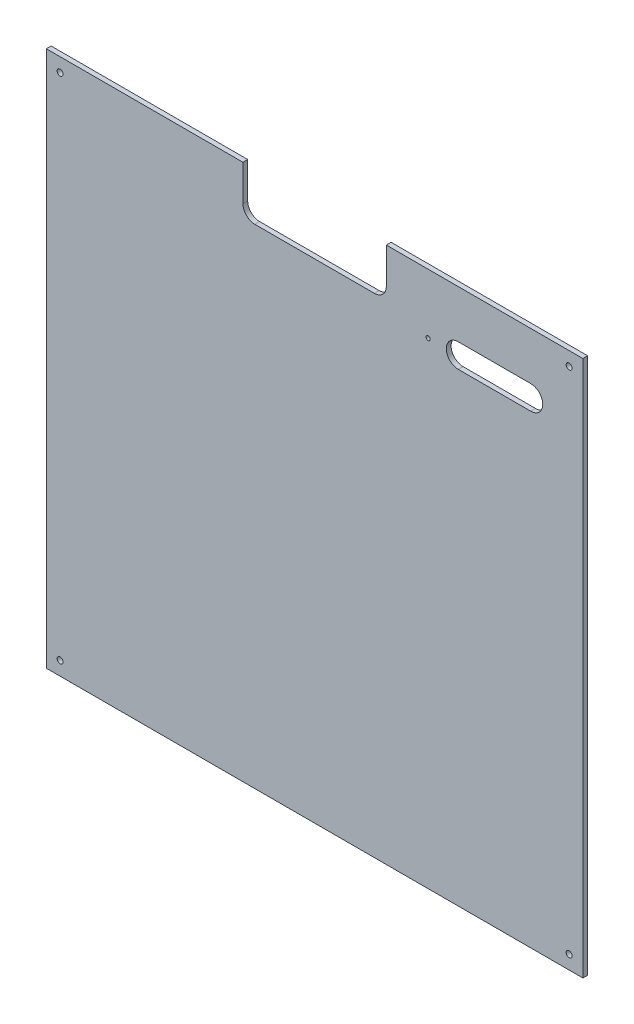
SolidWorks part; units mm, degrees
material "ABS PC"
ref_plane "Piano frontale" through (0, 0, 0) normal (0, 0, 1) x (1, 0, 0)
ref_plane "Piano superiore" through (0, 0, 0) normal (0, 1, 0) x (1, 0, 0)
ref_plane "Piano destro" through (0, 0, 0) normal (1, 0, 0) x (0, 0, -1)
sketch "Schizzo1" plane through (0, 0, 0) normal (0, 0, 1) x (1, 0, 0)
  line L0 (0, 0) -> (0, 449)
  line L1 (0, 449) -> (164.5, 449)
  line L2 (449, 449) -> (449, 0)
  line L3 (449, 0) -> (0, 0)
  line L4 (164.5, 449) -> (164.5, 419)
  line L5 (174.5, 409) -> (274.5, 409)
  line L6 (284.5, 419) -> (284.5, 449)
  line L7 (284.5, 449) -> (449, 449)
  line L8 (154.5, 399) -> (294.5, 399) construction
  line L9 (224.5, 379) -> (224.5, 419) construction
  line L10 (344.7159, 399) -> (405.4404, 399) construction
  line L11 (344.7159, 409) -> (405.4404, 409)
  line L12 (344.7159, 389) -> (405.4404, 389)
  line L13 (0, 224.5) -> (449, 224.5) construction
  line L23 (73.9219, 399) -> (73.9219, 449) construction
  line L24 (164.5, 434) -> (304.5, 434) construction
  arc A0 (164.5, 419) -> (174.5, 409) centre (174.5, 419) ccw
  arc A1 (284.5, 419) -> (274.5, 409) centre (274.5, 419) cw
  circle A2 centre (11.5, 11.5) radius 2.5
  circle A3 centre (437.5, 11.5) radius 2.5
  circle A4 centre (437.5, 437.5) radius 2.5
  circle A5 centre (11.5, 437.5) radius 2.5
  circle A6 centre (319.5, 399) radius 1.75
  arc A8 (344.7159, 409) -> (344.7159, 389) centre (344.7159, 399) ccw
  arc A9 (405.4404, 389) -> (405.4404, 409) centre (405.4404, 399) ccw
  point P11 (164.5, 409)
  point P14 (284.5, 409)
  point P33 (375.0781, 399)
  dimension "D5" = 10
  dimension "D6" = 11.5
  dimension "D7" = 11.5
  dimension "D8" = 5
  dimension "D9" = 3.5
  dimension "D10" = 35
  dimension "D1" = 449
  dimension "D2" = 449
  dimension "D3" = 120
  dimension "D4" = 40
  dimension "D11" = 20
  dimension "D21" = 50
extrude "Estrusione-Estrusione1" add sketch "Schizzo1" along normal blind 4
